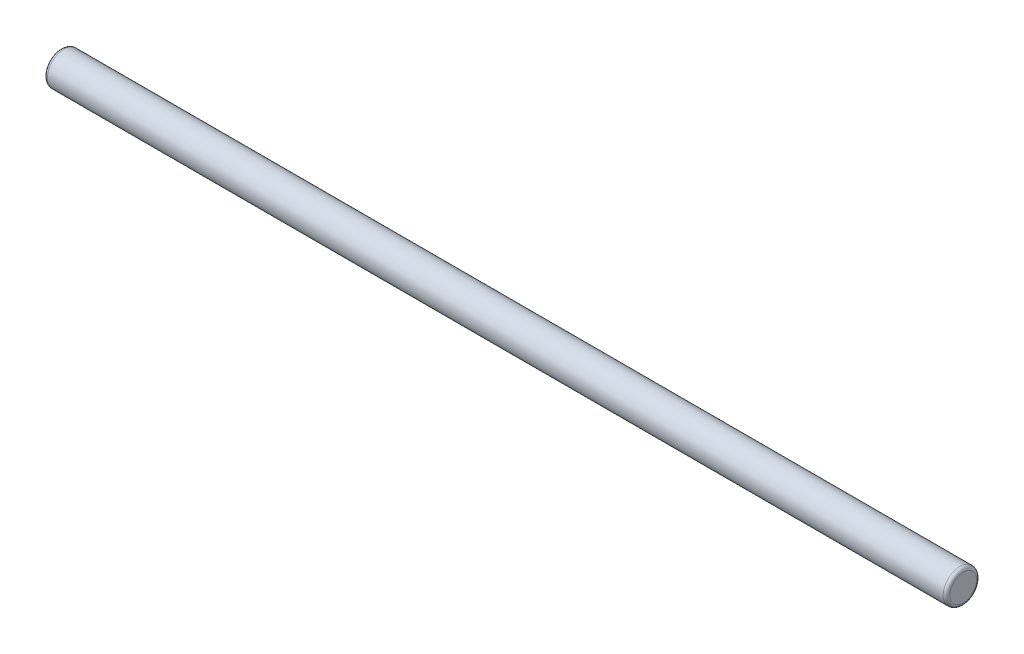
SolidWorks part; units mm, degrees
ref_plane "Front Plane" through (0, 0, 0) normal (0, 0, 1) x (1, 0, 0)
ref_plane "Top Plane" through (0, 0, 0) normal (0, 1, 0) x (1, 0, 0)
ref_plane "Right Plane" through (0, 0, 0) normal (1, 0, 0) x (0, 0, -1)
sketch "Sketch1" plane through (0, 0, 0) normal (1, 0, 0) x (0, 0, -1)
  circle A0 centre (0, 0) radius 5
extrude "Boss-Extrude1" add sketch "Sketch1" along normal blind 270
fillet "Fillet1" radius 1 2 edges at (270, 0, -5) (0, 0, -5)
